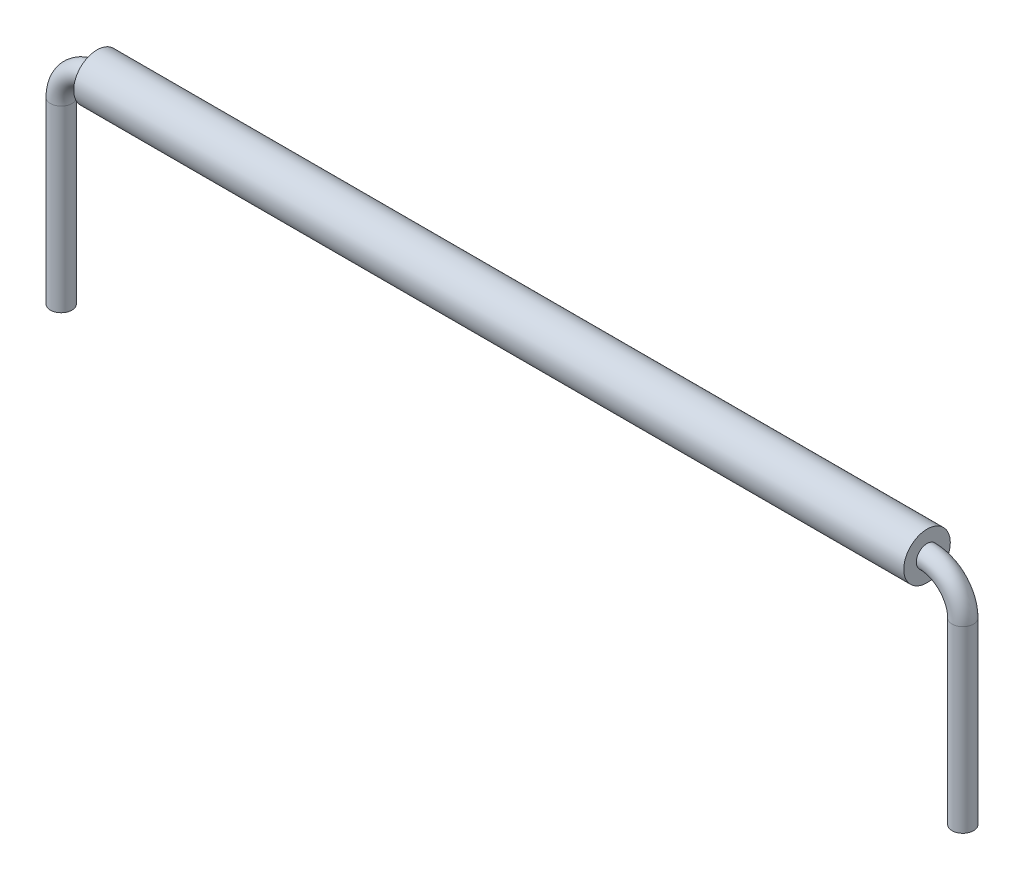
SolidWorks part; units mm, degrees
other "Insulation"
other "Wire"
ref_plane "Front Plane" through (0, 0, 0) normal (0, 0, 1) x (1, 0, 0)
ref_plane "Top Plane" through (0, 0, 0) normal (0, 1, 0) x (1, 0, 0)
ref_plane "Right Plane" through (0, 0, 0) normal (1, 0, 0) x (0, 0, -1)
sketch "Sketch1" plane through (0, 0, 0) normal (0, 0, 1) x (1, 0, 0)
  line L0 (-11.596, 0) -> (11.596, 0)
  line L1 (-12.596, -1) -> (-12.596, -6)
  line L2 (12.596, -1) -> (12.596, -6)
  line L3 (0, 0) -> (0, -6) construction
  line L4 (-12.596, -6) -> (12.596, -6) construction
  arc A0 (-11.596, 0) -> (-12.596, -1) centre (-11.596, -1) ccw
  arc A1 (11.596, 0) -> (12.596, -1) centre (11.596, -1) cw
  dimension "D1" = 1
  dimension "D2" = 25.192
  dimension "D3" = 6
sketch "Sketch2" plane through (0, 0, 0) normal (1, 0, 0) x (0, 0, -1)
  circle A0 centre (0, 0) radius 0.3
  dimension "D1" = 0.6
sweep "Sweep1" add profiles "Sketch2" path "Sketch1"
sketch "Sketch3" plane through (0, 0, 0) normal (1, 0, 0) x (0, 0, -1)
  circle A0 centre (0, 0) radius 0.65
  circle A1 centre (0, 0) radius 0.3
  dimension "D1" = 1.3
  dimension "D2" = 0.6
extrude "Boss-Extrude1" add sketch "Sketch3" along normal up to vertex (11.596 mm away) and the other way up to vertex (11.596 mm away) separate body up to point (11.596, 0, 0) other way up to point (-11.596, 0, 0)
